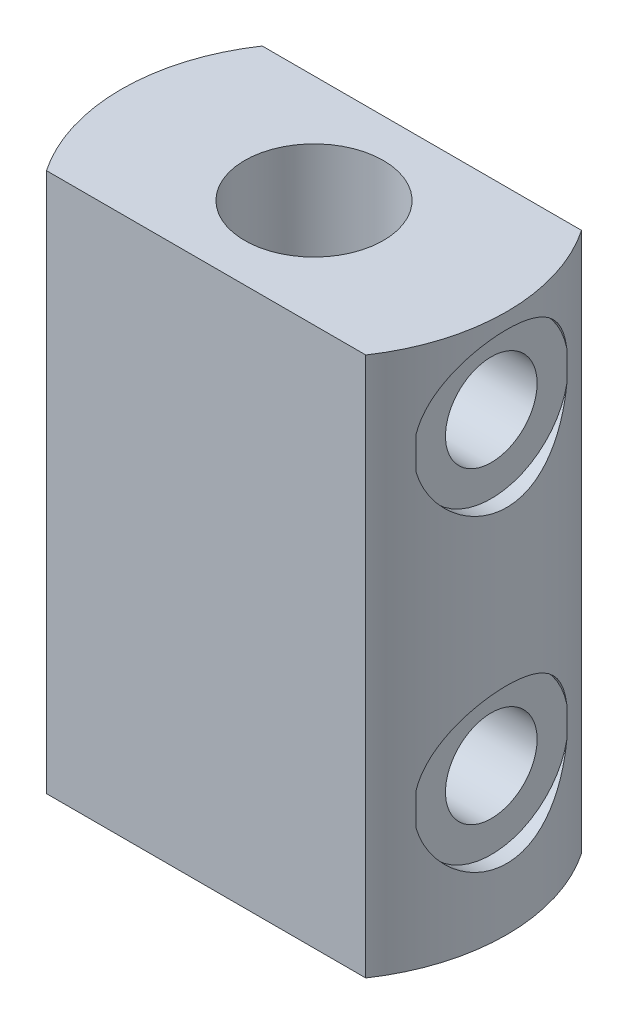
SolidWorks part; units mm, degrees
material "Liga de aço (SS)"
ref_plane "Plano frontal" through (0, 0, 0) normal (0, 0, 1) x (1, 0, 0)
ref_plane "Plano superior" through (0, 0, 0) normal (0, 1, 0) x (1, 0, 0)
ref_plane "Plano direito" through (0, 0, 0) normal (1, 0, 0) x (0, 0, -1)
sketch "Esboço1" plane through (0, 0, 0) normal (0, 0, 1) x (1, 0, 0)
  line L0 (0, 0) -> (0, 8710.2202) construction
  line L1 (0, 0) -> (8710.2202, 0) construction
  line L2 (9, 32) -> (25, 32)
  line L3 (25, 32) -> (25, -38)
  line L4 (25, -38) -> (0, -38)
  line L5 (0, -38) -> (0, -34)
  line L6 (0, -34) -> (9, -34)
  line L7 (9, -34) -> (9, 32)
  dimension "D1" = 18
  dimension "D2" = 50
  dimension "D3" = 32
  dimension "D4" = 4
  dimension "D6" = 34
revolve "Revolução1" add sketch "Esboço1" angle 360 about L0
hole_wizard "Furo roscado de 1/4-18 NPSM1" positions "3DSketch1" profile "Esboço2" tap size "1/4-18 NPSM" standard "Ansi Inch"
sketch3d "3DSketch1"
  point P0 (-25, 0, 0)
sketch "Esboço2" plane through (-25, 0, 0) normal (0, 1, 0) x (0, 0, 1)
  line L0 (0, 0) -> (0, 16)
  line L1 (0, 16) -> (5.9436, 16)
  line L2 (5.9436, 16) -> (5.9436, 0)
  line L5 (5.9436, 0) -> (0, 0)
  line L11 (0, -6.35) -> (0, 107.95) construction
  dimension "Thru Tap Drill Dia." = 11.8872
  dimension "Thru Tap Drill Depth" = 16
cosmetic thread "Rosca de furo1" parameters "D2"=13.3604
hole_wizard "Furo roscado de 1/4-18 NPSM2" positions "3DSketch2" profile "Esboço3" tap size "1/4-18 NPSM" standard "Ansi Inch"
sketch3d "3DSketch2"
  line L4 (0, 0, 0) -> (0, 20, 0) construction
  line L5 (0, 20, 0) -> (25, 20, 0) construction
  line L7 (0, 0, 0) -> (0, -20, 0) construction
  line L8 (0, -20, 0) -> (25, -20, 0) construction
  point P0 (25, 20, 0)
  point P2 (25, -20, 0)
  dimension "D1" = 20
  dimension "D2" = 20
sketch "Esboço3" plane through (25, 20, 0) normal (0, 1, 0) x (0, 0, -1)
  line L0 (0, 0) -> (0, 16)
  line L1 (0, 16) -> (5.9436, 16)
  line L2 (5.9436, 16) -> (5.9436, 0)
  line L5 (5.9436, 0) -> (0, 0)
  line L11 (0, -6.35) -> (0, 107.95) construction
  dimension "Thru Tap Drill Dia." = 11.8872
  dimension "Thru Tap Drill Depth" = 16
cosmetic thread "Rosca de furo2" parameters "D2"=13.3604
cosmetic thread "Rosca de furo3" parameters "D2"=13.3604
ref_plane "Plano1" through (-25, 0, 0) normal (-1, 0, 0) x (0, 0, 1)
ref_plane "Plano2" through (25, 0, 0) normal (1, 0, 0) x (0, 0, -1)
sketch "Esboço4" plane through (-25, 0, 0) normal (1, 0, 0) x (0, 0, -1)
  circle A0 centre (0, 0) radius 10
  dimension "D1" = 20
extrude "Corte-extrusão1" cut sketch "Esboço4" along normal blind 2
sketch "Esboço6" plane through (25, 0, 0) normal (1, 0, 0) x (0, 0, -1)
  circle A0 centre (0, 20) radius 10
  circle A1 centre (0, -20) radius 10
  circle A2 centre (0, 0) radius 10 construction
extrude "Corte-extrusão2" cut sketch "Esboço6" against normal blind 2
sketch "Esboço7" plane through (0, 32, 0) normal (0, 1, 0) x (1, 0, 0)
  line L0 (-20.7123, 14) -> (20.7123, 14)
  line L1 (0, 0) -> (50000, 0) construction
  line L2 (-20.7123, -14) -> (20.7123, -14)
  circle A0 centre (0, 0) radius 25 construction
  arc A1 (20.7123, 14) -> (-20.7123, 14) centre (0, 0) ccw
  arc A2 (20.7123, -14) -> (-20.7123, -14) centre (0, 0) cw
  dimension "D1" = 14
extrude "Corte-extrusão3" cut sketch "Esboço7" against normal through all
